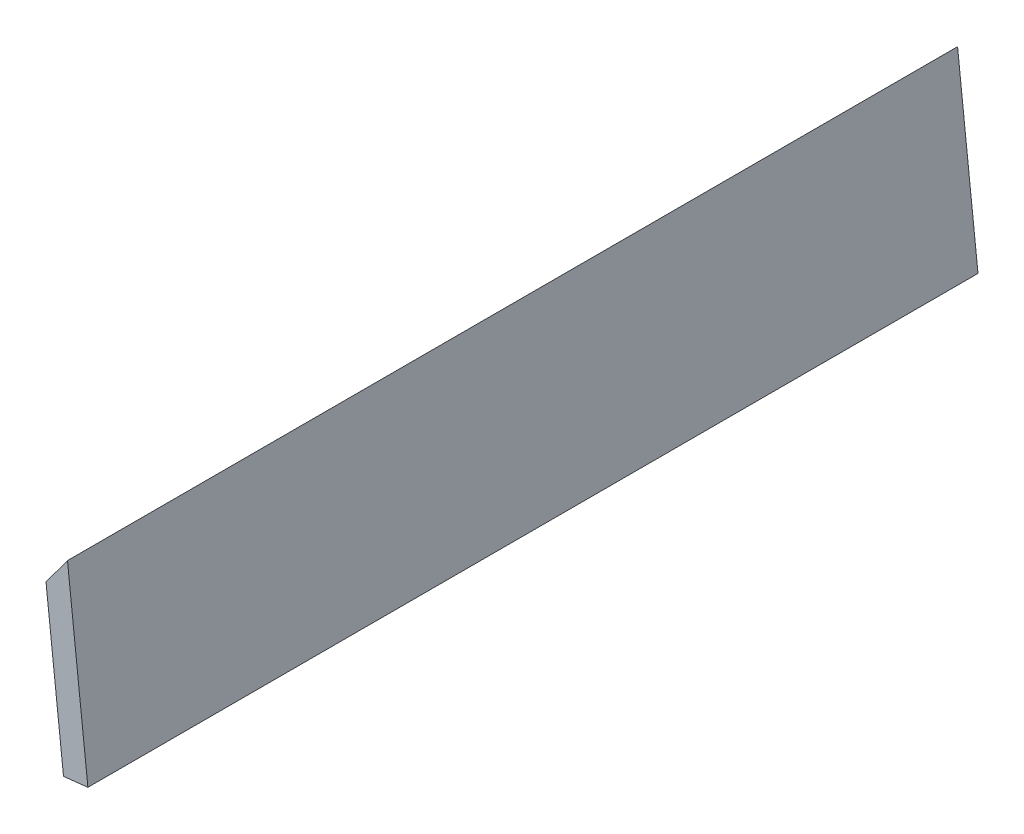
SolidWorks part; units mm, degrees
ref_plane "Front Plane" through (0, 0, 0) normal (0, 0, 1) x (1, 0, 0)
ref_plane "Top Plane" through (0, 0, 0) normal (0, 1, 0) x (1, 0, 0)
ref_plane "Right Plane" through (0, 0, 0) normal (1, 0, 0) x (0, 0, -1)
sketch "Sketch1" plane through (0, 0, 0) normal (0, 0, 1) x (1, 0, 0)
  line L0 (-25, -19.5854) -> (-17.2006, -8.9515) construction
  line L2 (-17.2006, -8.9515) -> (-15.8879, -7.1618)
  line L3 (-15.8879, -7.1618) -> (-14.4358, -20.3995) construction
  line L4 (0, -0.7175) -> (-17.7428, -24.9083) construction
  line L5 (-17.2006, -8.9515) -> (-15.2379, -26.8442)
  line L6 (-15.8879, -7.1618) -> (-14.7933, -5.6695)
  line L7 (-14.7933, -5.6695) -> (-12.5036, -26.5443)
  line L8 (-15.2379, -26.8442) -> (-12.5036, -26.5443)
  dimension "D1" = 3
  dimension "D4" = 21
extrude "Boss-Extrude1" add sketch "Sketch1" along normal offset from surface (99.8 mm away) 6
